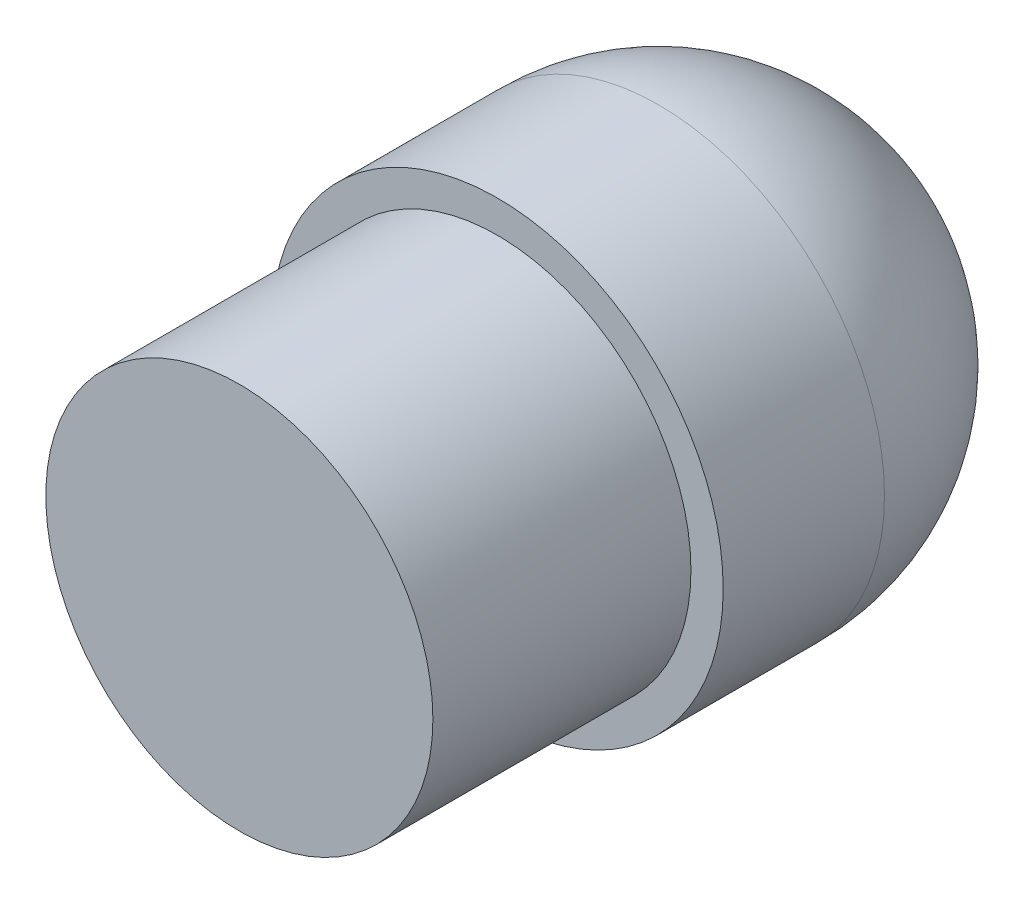
SolidWorks part; units mm, degrees
ref_plane "Alzado" through (0, 0, 0) normal (0, 0, 1) x (1, 0, 0)
ref_plane "Planta" through (0, 0, 0) normal (0, 1, 0) x (1, 0, 0)
ref_plane "Vista lateral" through (0, 0, 0) normal (1, 0, 0) x (0, 0, -1)
sketch "Croquis1" plane through (0, 0, 0) normal (1, 0, 0) x (0, 0, -1)
  line L0 (0, 0) -> (102.7919, 0) construction
  line L1 (0, 0) -> (0, 15)
  line L2 (0, 15) -> (20, 15)
  line L3 (20, 15) -> (20, 17.5)
  line L4 (20, 17.5) -> (32.5, 17.5)
  line L5 (0, 0) -> (50, 0)
  arc A0 (32.5, 17.5) -> (50, 0) centre (32.5, 0) cw
  point P9 (0, 0)
  point P10 (0, 0)
  dimension "D4" = 17.5
  dimension "D1" = 30
  dimension "D2" = 50
  dimension "D3" = 20
revolve "Revolución1" add sketch "Croquis1" angle 360 about L0
